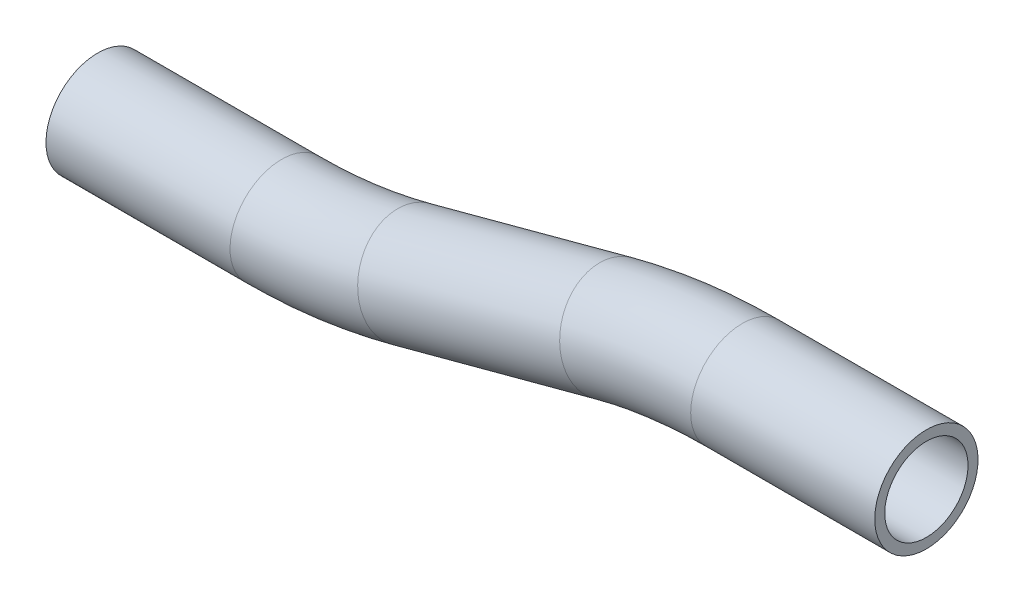
SolidWorks part; units mm, degrees
material "6061 Alloy"
ref_plane "Front Plane" through (0, 0, 0) normal (0, 0, 1) x (1, 0, 0)
ref_plane "Top Plane" through (0, 0, 0) normal (0, 1, 0) x (1, 0, 0)
ref_plane "Right Plane" through (0, 0, 0) normal (1, 0, 0) x (0, 0, -1)
sketch "Sketch1" plane through (0, 0, 0) normal (0, 0, 1) x (1, 0, 0)
  line L0 (0, 0) -> (28.0681, 0)
  line L2 (-19.722, -2.5965) -> (-50.524, -10.8498)
  line L3 (-50.524, -10.8498) -> (-10.0319, 0)
  line L4 (28.0681, 0) -> (-10.0319, 0)
  line L5 (-70.246, -13.4463) -> (-98.3141, -13.4463)
  line L6 (-98.3141, -13.4463) -> (-60.2141, -13.4463)
  line L7 (-19.722, -2.5965) -> (-60.2141, -13.4463)
  arc A0 (0, 0) -> (-19.722, -2.5965) centre (0, -76.2) ccw
  arc A1 (-50.524, -10.8498) -> (-70.246, -13.4463) centre (-70.246, 62.7537) cw
  point P9 (-10.0319, 0)
  point P14 (-60.2141, -13.4463)
  dimension "D3" = 15
  dimension "D4" = 15
  dimension "D1" = 76.2
  dimension "D2" = 76.2
  dimension "D5" = 51.9524
  dimension "D6" = 38.1
  dimension "D7" = 38.1
ref_plane "Plane1" through (28.0681, 0, 0) normal (-1, 0, 0) x (0, 0, 1)
sketch "Sketch2" plane through (28.0681, 0, 0) normal (-1, 0, 0) x (0, 0, 1)
  circle A0 centre (0, 0) radius 6.35
  circle A1 centre (0, 0) radius 7.874
  dimension "D1" = 12.7
  dimension "D2" = 15.748
sweep "Sweep1" add profiles "Sketch2" path "Sketch1"
